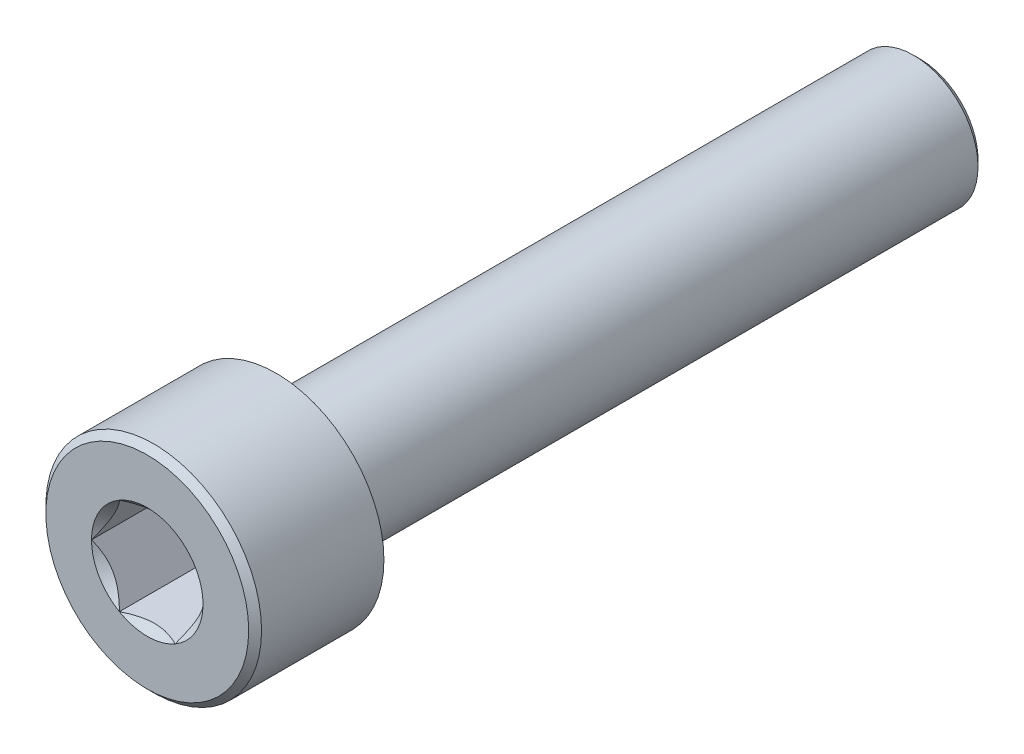
SolidWorks part; units mm, degrees
ref_plane "Спереди" through (0, 0, 0) normal (0, 0, 1) x (1, 0, 0)
ref_plane "Сверху" through (0, 0, 0) normal (0, 1, 0) x (1, 0, 0)
ref_plane "Справа" through (0, 0, 0) normal (1, 0, 0) x (0, 0, -1)
sketch "Эскиз1" plane through (0, 0, 0) normal (0, 0, 1) x (1, 0, 0)
  circle A1 centre (0, 0) radius 3.35
extrude "Бобышка-Вытянуть1" add sketch "Эскиз1" along normal blind 4
sketch "Эскиз2" plane through (0, 0, 4) normal (0, 0, 1) x (1, 0, 0)
  line L1 (1.7321, 0) -> (0.866, 1.5)
  line L2 (0.866, 1.5) -> (-0.866, 1.5)
  line L3 (-0.866, 1.5) -> (-1.7321, 0)
  line L4 (-1.7321, 0) -> (-0.866, -1.5)
  line L5 (-0.866, -1.5) -> (0.866, -1.5)
  line L6 (0.866, -1.5) -> (1.7321, 0)
  circle A0 centre (0, 0) radius 1.5 construction
extrude "Вырез-Вытянуть1" cut sketch "Эскиз2" against normal blind 2.8
sketch "Эскиз3" plane through (0, 0, 0) normal (0, 0, -1) x (-1, 0, 0)
  circle A0 centre (0, 0) radius 2
extrude "Бобышка-Вытянуть2" add sketch "Эскиз3" along normal blind 20
sketch "Эскиз4" plane through (0, 0, 4) normal (0, 0, 1) x (1, 0, 0)
  circle A0 centre (0, 0) radius 1.7321
extrude "Вырез-Вытянуть2" cut sketch "Эскиз4" against normal blind 2 draft 45
chamfer "Фаска1" distance 0.2 angle 45 2 edges at (-2, 0, -20) (3.35, 0, 4)
